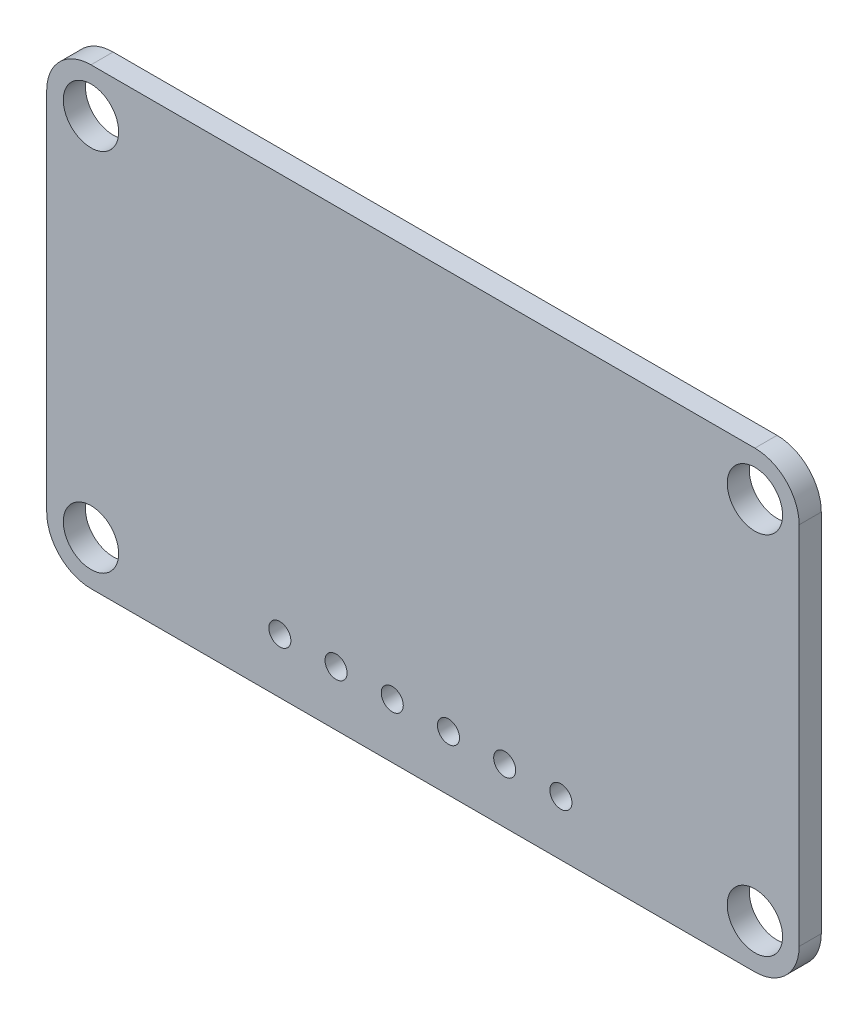
SolidWorks part; units mm, degrees
ref_plane "Front Plane" through (0, 0, 0) normal (0, 0, 1) x (1, 0, 0)
ref_plane "Top Plane" through (0, 0, 0) normal (0, 1, 0) x (1, 0, 0)
ref_plane "Right Plane" through (0, 0, 0) normal (1, 0, 0) x (0, 0, -1)
sketch "Sketch1" plane through (0, 0, 0) normal (0, 0, 1) x (1, 0, 0)
  line L0 (-15.24, 10.34) -> (18.76, 10.34)
  line L1 (18.76, 10.34) -> (18.76, -10.16)
  line L2 (18.76, -10.16) -> (-15.24, -10.16)
  line L3 (-15.24, -10.16) -> (-15.24, 10.34)
extrude "Component_Outline" add sketch "Sketch1" along normal blind 1 separate body
sketch3d "3DSketch1"
  line L0 (0, 0, 0) -> (1, 0, 0)
  line L1 (0, 0, 0) -> (0, 1, 0)
  line L2 (0, 0, 0) -> (0, 0, 1)
  point P0 (0, 0, 0)
sketch "Sketch4" plane through (0, 0, 1) normal (0, 0, 1) x (1, 0, 0)
  circle A0 centre (-4.7061, -7.6756) radius 0.4983
  circle A1 centre (-2.1661, -7.6756) radius 0.4983
  circle A2 centre (0.3739, -7.6756) radius 0.4983
  circle A3 centre (2.9139, -7.6756) radius 0.4983
  circle A4 centre (5.4539, -7.6756) radius 0.4983
  circle A5 centre (7.9939, -7.6756) radius 0.4983
  dimension "D1" = 6
extrude "Cut-Extrude1" cut sketch "Sketch4" against normal up to next contours A0 | A1 | A2 | A3 | A4 | A5
sketch "Sketch5" plane through (0, 0, 1) normal (0, 0, 1) x (1, 0, 0)
  line L0 (-15.24, 10.34) -> (-15.24, -10.16) construction
  line L1 (18.76, 10.34) -> (-15.24, 10.34) construction
  circle A0 centre (-13.24, 8.34) radius 1.25
  circle A1 centre (-13.24, -8.16) radius 1.25
  circle A2 centre (16.76, 8.34) radius 1.25
  circle A3 centre (16.76, -8.16) radius 1.25
  dimension "D1" = 2.5
  dimension "D3" = 2
  dimension "D4" = 2.5
  dimension "D5" = 2
  dimension "D6" = 18.5
  dimension "D7" = 2.5
  dimension "D8" = 2
  dimension "D9" = 32
  dimension "D10" = 2.5
  dimension "D11" = 32
  dimension "D12" = 18.5
  dimension "D2" = 2
extrude "Cut-Extrude2" cut sketch "Sketch5" against normal through all contours A0 | A2 | A3 | A1
fillet "Fillet1" radius 2 4 edges at (18.76, 10.34, 0.5) (18.76, -10.16, 0.5) (-15.24, 10.34, 0.5) (-15.24, -10.16, 0.5)
